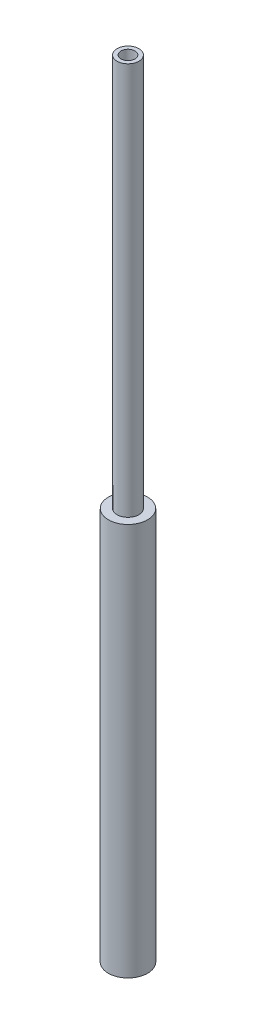
SolidWorks part; units mm, degrees
ref_plane "Front Plane" through (0, 0, 0) normal (0, 0, 1) x (1, 0, 0)
ref_plane "Top Plane" through (0, 0, 0) normal (0, 1, 0) x (1, 0, 0)
ref_plane "Right Plane" through (0, 0, 0) normal (1, 0, 0) x (0, 0, -1)
sketch "Sketch1" plane through (0, 0, 0) normal (0, 1, 0) x (1, 0, 0)
  circle A0 centre (0, 0) radius 0.889
  circle A1 centre (0, 0) radius 1.389
  dimension "D1" = 1.778
  dimension "D2" = 0.5
extrude "Boss-Extrude1" add sketch "Sketch1" along normal blind 100
sketch "Sketch2" plane through (0, 0, 0) normal (0, 1, 0) x (1, 0, 0)
  circle A0 centre (0, 0) radius 2.5
  dimension "D1" = 5
extrude "Boss-Extrude2" add sketch "Sketch2" along normal blind 50
